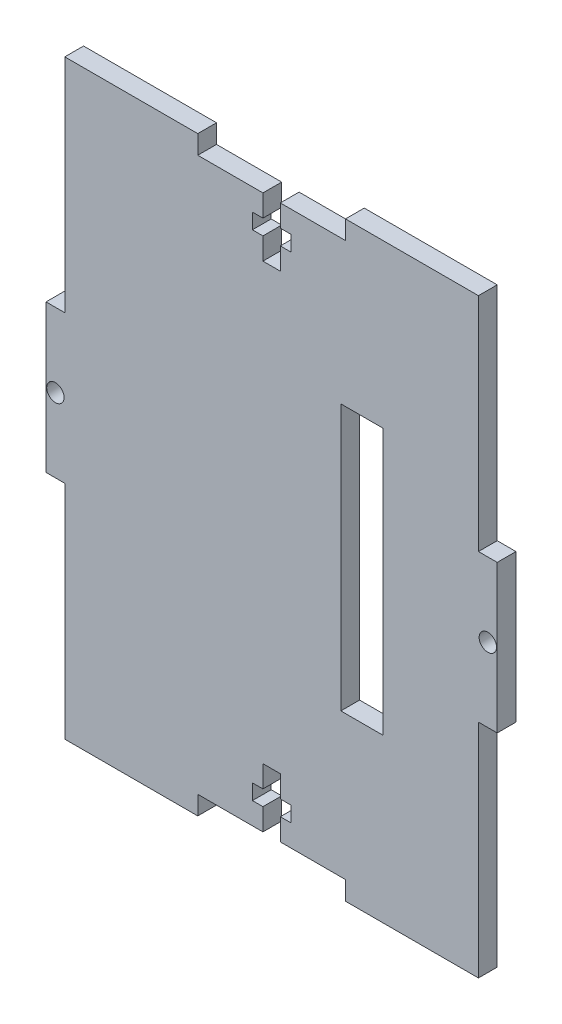
SolidWorks part; units mm, degrees
ref_plane "Front Plane" through (0, 0, 0) normal (0, 0, 1) x (1, 0, 0)
ref_plane "Top Plane" through (0, 0, 0) normal (0, 1, 0) x (1, 0, 0)
ref_plane "Right Plane" through (0, 0, 0) normal (1, 0, 0) x (0, 0, -1)
sketch "Sketch1" plane through (0, 0, 0) normal (0, 0, 1) x (1, 0, 0)
  line L0 (0, 50) -> (0, -50) construction
  line L1 (-35, 50) -> (35, 50)
  line L2 (-35, 50) -> (-35, -50)
  line L3 (-35, -50) -> (35, -50)
  line L4 (35, 50) -> (35, -50)
  line L5 (-35, 50) -> (35, -50) construction
  line L6 (-35, -50) -> (35, 50) construction
  line L7 (-35, 0) -> (35, 0) construction
  line L8 (-3.25, -40.525) -> (3.25, -40.525)
  line L9 (12.5, 50) -> (-12.5, 50)
  line L10 (12.5, 50) -> (12.5, 46.825)
  line L11 (12.5, 46.825) -> (-12.5, 46.825)
  line L12 (-12.5, 50) -> (-12.5, 46.825)
  line L13 (12.5, 50) -> (-12.5, 46.825) construction
  line L14 (12.5, 46.825) -> (-12.5, 50) construction
  line L15 (-1.47, 46.825) -> (1.47, 46.825)
  line L16 (-1.47, 46.825) -> (-1.47, 36.825)
  line L17 (-1.47, 36.825) -> (1.47, 36.825)
  line L18 (1.47, 46.825) -> (1.47, 36.825)
  line L19 (-1.47, 46.825) -> (1.47, 36.825) construction
  line L20 (-1.47, 36.825) -> (1.47, 46.825) construction
  line L21 (-3.25, 43.125) -> (3.25, 43.125)
  line L22 (-3.25, 43.125) -> (-3.25, 40.525)
  line L23 (-3.25, 40.525) -> (3.25, 40.525)
  line L24 (3.25, 43.125) -> (3.25, 40.525)
  line L25 (-3.25, 43.125) -> (3.25, 40.525) construction
  line L26 (-3.25, 40.525) -> (3.25, 43.125) construction
  line L27 (3.25, -43.125) -> (3.25, -40.525)
  line L28 (-3.25, -43.125) -> (3.25, -43.125)
  line L29 (-3.25, -43.125) -> (-3.25, -40.525)
  line L30 (-1.47, -36.825) -> (1.47, -36.825)
  line L31 (1.47, -46.825) -> (1.47, -36.825)
  line L32 (-1.47, -46.825) -> (1.47, -46.825)
  line L33 (-1.47, -46.825) -> (-1.47, -36.825)
  line L34 (12.5, -46.825) -> (-12.5, -46.825)
  line L35 (-12.5, -50) -> (-12.5, -46.825)
  line L36 (12.5, -50) -> (-12.5, -50)
  line L37 (12.5, -50) -> (12.5, -46.825)
  line L38 (38.175, -12.5) -> (35, -12.5)
  line L39 (-38.175, 12.5) -> (-35, 12.5)
  line L40 (-38.175, 12.5) -> (-38.175, -12.5)
  line L41 (-38.175, -12.5) -> (-35, -12.5)
  line L42 (-35, 12.5) -> (-35, -12.5)
  line L43 (-38.175, 12.5) -> (-35, -12.5) construction
  line L44 (-38.175, -12.5) -> (-35, 12.5) construction
  line L45 (35, 12.5) -> (35, -12.5)
  line L46 (38.175, 12.5) -> (35, 12.5)
  line L47 (38.175, 12.5) -> (38.175, -12.5)
  circle A0 centre (-36.5875, 0) radius 1.47
  circle A1 centre (36.5875, 0) radius 1.47
  point P0 (0, 0)
  point P10 (0, 48.4125)
  point P15 (0, 41.825)
  point P20 (0, 41.825)
  point P37 (-36.5875, 0)
  dimension "D11" = 2.94
  dimension "D1" = 100
  dimension "D2" = 70
  dimension "D3" = 3.175
  dimension "D4" = 10
  dimension "D5" = 2.94
  dimension "D6" = 25
  dimension "D7" = 6.5
  dimension "D8" = 2.6
  dimension "D9" = 6.3
  dimension "D10" = 3.175
extrude "Boss-Extrude1" add sketch "Sketch1" along normal mid plane 3.175 contours L21 L24 L23 L18 L17 L16 L22 L11 L12 L1 L2 L3 L4 L10 | L40 L39 L42 L41 | A0 | L38 L45 L46 L47 | A1
sketch "Sketch3" plane through (0, 0, -1.5875) normal (0, 0, -1) x (-1, 0, 0)
  line L0 (-16.8875, 25) -> (-16.8875, -25) construction
  line L1 (-11.7125, 22.5) -> (-18.8875, 22.5)
  line L2 (-11.7125, 22.5) -> (-11.7125, -22.5)
  line L3 (-11.7125, -22.5) -> (-18.8875, -22.5)
  line L4 (-18.8875, 22.5) -> (-18.8875, -22.5)
  line L5 (-13.7125, -25) -> (-13.7125, 25) construction
  line L6 (0, 0) -> (-7.5076, 0) construction
  dimension "D1" = 2
  dimension "D2" = 2
  dimension "D3" = 45
extrude "Cut-Extrude1" cut sketch "Sketch3" against normal through all
